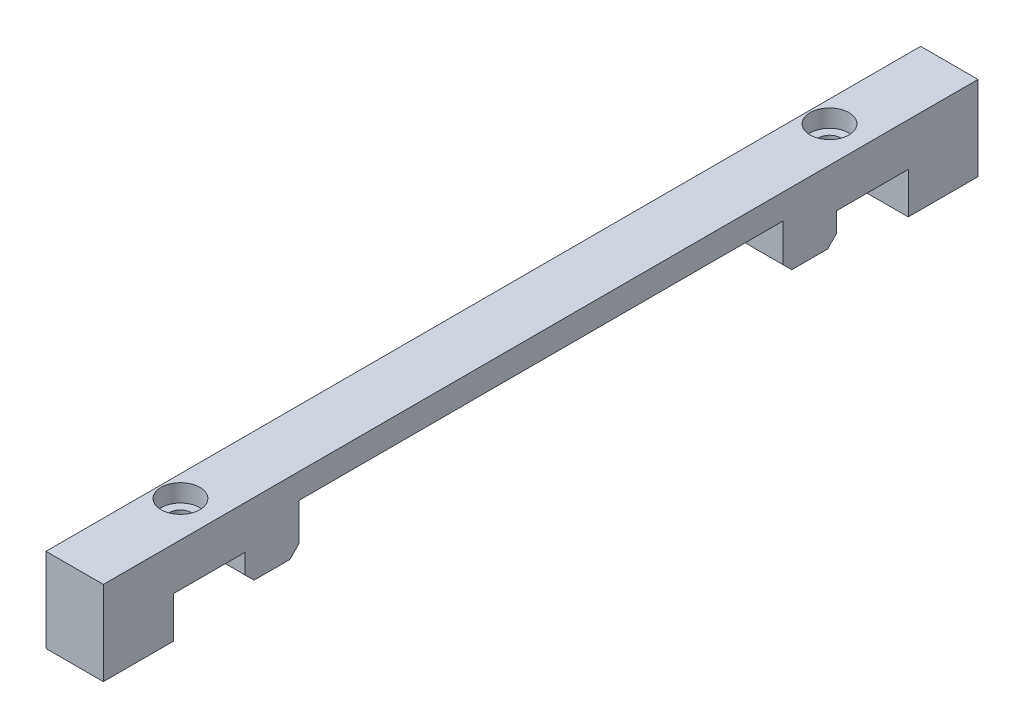
SolidWorks part; units mm, degrees
ref_plane "Front Plane" through (0, 0, 0) normal (0, 0, 1) x (1, 0, 0)
ref_plane "Top Plane" through (0, 0, 0) normal (0, 1, 0) x (1, 0, 0)
ref_plane "Right Plane" through (0, 0, 0) normal (1, 0, 0) x (0, 0, -1)
sketch "Sketch1" plane through (0, 0, 0) normal (0, 1, 0) x (1, 0, 0)
  line L1 (-4.064, 63.5) -> (4.064, 63.5)
  line L2 (-4.064, 63.5) -> (-4.064, -63.5)
  line L3 (-4.064, -63.5) -> (4.064, -63.5)
  line L4 (4.064, 63.5) -> (4.064, -63.5)
  line L5 (-4.064, 63.5) -> (4.064, -63.5) construction
  line L6 (-4.064, -63.5) -> (4.064, 63.5) construction
  point P0 (0, 0)
  dimension "D1" = 127
  dimension "D2" = 8.128
extrude "Boss-Extrude1" add sketch "Sketch1" along normal blind 18.288
sketch "Sketch2" plane through (0, 0, 0) normal (0, -1, 0) x (1, 0, 0)
  line L0 (4.064, 63.5) -> (4.064, -63.5) construction
  line L1 (-4.064, 52.07) -> (4.064, 52.07)
  line L2 (-4.064, 52.07) -> (-4.064, -52.07)
  line L3 (-4.064, -52.07) -> (4.064, -52.07)
  line L4 (4.064, 52.07) -> (4.064, -52.07)
  line L5 (-4.064, 52.07) -> (4.064, -52.07) construction
  line L6 (-4.064, -52.07) -> (4.064, 52.07) construction
  point P0 (0, 0)
  dimension "D1" = 104.14
extrude "Cut-Extrude1" cut sketch "Sketch2" against normal blind 8.128
sketch "Sketch4" plane through (0, 8.128, 0) normal (0, -1, 0) x (1, 0, 0)
  line L1 (-4.064, -41.91) -> (4.064, -41.91)
  line L2 (-4.064, -41.91) -> (-4.064, -52.07)
  line L3 (-4.064, -52.07) -> (4.064, -52.07)
  line L4 (4.064, -41.91) -> (4.064, -52.07)
  line L5 (-4.064, -41.91) -> (4.064, -52.07) construction
  line L6 (-4.064, -52.07) -> (4.064, -41.91) construction
  point P0 (0, -46.99)
  dimension "D1" = 10.16
extrude "Cut-Extrude2" cut sketch "Sketch4" against normal blind 4.064
sketch "Sketch5" plane through (0, 8.128, 0) normal (0, -1, 0) x (1, 0, 0)
  line L0 (4.064, -41.91) -> (4.064, 52.07) construction
  line L5 (4.064, 0) -> (-4.064, 0)
  line L6 (4.064, 0) -> (4.064, -34.29)
  line L8 (4.064, -34.29) -> (-4.064, -34.29)
  line L9 (-4.064, 0) -> (-4.064, -34.29)
  line L10 (4.064, -41.91) -> (-4.064, -41.91) construction
  dimension "D1" = 7.62
extrude "Cut-Extrude4" cut sketch "Sketch5" against normal blind 6.604
sketch "Sketch6" plane through (0, 18.288, 0) normal (0, 1, 0) x (1, 0, 0)
  line L1 (4.064, -63.5) -> (4.064, 63.5) construction
  line L3 (-4.064, 52.07) -> (4.064, 52.07) construction
  point P0 (-1.016, 46.99)
  dimension "D1" = 5.08
  dimension "D2" = 5.08
hole_wizard "CBORE for M2.5 SHCS1" positions "Sketch7" profile "Sketch8" counterbore size "M2.5" standard "ANSI Metric" end condition through all
sketch "Sketch7" plane through (0, 18.288, 0) normal (0, 1, 0) x (1, 0, 0)
  line L0 (4.064, -63.5) -> (4.064, 63.5) construction
  line L5 (-4.064, 45.99) -> (4.064, 45.99) construction
  line L9 (-4.064, 52.07) -> (4.064, 52.07) construction
  point P0 (-1.016, 45.99)
  dimension "D1" = 5.08
  dimension "D2" = 6.08
sketch "Sketch8" plane through (-1.016, 18.288, -45.99) normal (1, 0, 0) x (0, 0, 1)
  line L0 (0, 0) -> (0, 18.288)
  line L1 (0, 18.288) -> (1.55, 18.288)
  line L3 (1.55, 18.288) -> (1.55, 2.5)
  line L4 (1.55, 2.5) -> (2.75, 2.5)
  line L5 (2.75, 2.5) -> (2.75, 0)
  line L7 (2.75, 0) -> (0, 0)
  line L11 (0, -6.35) -> (0, 107.95) construction
  dimension "Thru Hole Dia." = 3.1
  dimension "Thru Hole Depth" = 18.288
  dimension "C'Bore Dia." = 5.5
  dimension "C'Bore Depth" = 2.5
mirror "Mirror1" about plane through (4.064, 14.732, 0) normal (0, 0, 1) of "Cut-Extrude4", "Cut-Extrude2"
mirror "Mirror2" about plane through (0, 0, 0) normal (0, 0, 1) of "CBORE for M2.5 SHCS1"
sketch "Sketch11" plane through (0, 0, 0) normal (0, -1, 0) x (1, 0, 0)
  line L0 (4.064, -57.785) -> (-4.064, -57.785) construction
  line L1 (4.064, -52.07) -> (4.064, -63.5) construction
  line L2 (-4.064, -63.5) -> (-4.064, -52.07) construction
  line L3 (0, -52.07) -> (0, -63.5) construction
  line L4 (-4.064, -52.07) -> (4.064, -52.07) construction
  line L5 (4.064, -63.5) -> (-4.064, -63.5) construction
  point P12 (0, -57.785)
hole_wizard "Ø1.0mm Dowel Hole1" positions "Sketch16" profile "Sketch15" hole size "Ø1.0" standard "ANSI Metric"
sketch "Sketch16" plane through (0, 0, 0) normal (0, -1, 0) x (-1, 0, 0)
  line L0 (-4.064, 57.785) -> (4.064, 57.785) construction
  line L1 (-4.064, 52.07) -> (-4.064, 63.5) construction
  line L2 (4.064, 63.5) -> (4.064, 52.07) construction
  line L4 (0, 63.5) -> (0, 52.07) construction
  line L5 (-4.064, 63.5) -> (4.064, 63.5) construction
  line L6 (4.064, 52.07) -> (-4.064, 52.07) construction
  point P0 (0, 57.785)
sketch "Sketch15" plane through (0, 0, -57.785) normal (1, 0, 0) x (0, 0, -1)
  line L0 (0, 0) -> (0, 11.9423)
  line L1 (0, 11.9423) -> (2.65, 10.35)
  line L2 (2.65, 10.35) -> (2.65, 0)
  line L5 (2.65, 0) -> (0, 0)
  line L10 (0, 11.9423) -> (-2.65, 10.35) construction
  line L11 (0, -6.35) -> (0, 107.95) construction
  dimension "Hole Dia." = 5.3
  dimension "Hole Depth" = 10.35
  dimension "Drill Angle" = 118
mirror "Mirror3" about plane through (0, 0, 0) normal (0, 0, 1) of "Ø1.0mm Dowel Hole1"
chamfer "Chamfer1" distance 1.27 angle 45 8 edges at (0, 0, 52.07) (0, 0, 63.5) (0, 8.128, 34.29) (0, 8.128, 41.91) (0, 8.128, -34.29) (0, 8.128, -41.91) (0, 0, -63.5) (0, 0, -52.07)
sketch "Sketch17" plane through (0, 0, 0) normal (0, -1, 0) x (1, 0, 0)
  line L5 (-4.064, 63.5) -> (4.064, 63.5)
  line L6 (-4.064, 63.5) -> (-4.064, -63.5)
  line L7 (-4.064, -63.5) -> (4.064, -63.5)
  line L8 (4.064, 63.5) -> (4.064, -63.5)
extrude "Cut-Extrude5" cut sketch "Sketch17" against normal blind 6.35
sketch "Sketch18" plane through (0, 6.35, 0) normal (0, -1, 0) x (1, 0, 0)
  line L0 (4.064, -63.5) -> (4.064, -61.9536)
  line L1 (4.064, -63.5) -> (4.064, -52.07) construction
  line L2 (4.064, -61.9536) -> (-4.064, -61.9536)
  line L3 (-4.064, -52.07) -> (-4.064, -63.5) construction
  line L4 (-4.064, -61.9536) -> (-4.064, -63.5)
  line L5 (-4.064, -63.5) -> (4.064, -63.5)
extrude "Cut-Extrude6" cut sketch "Sketch18" against normal through all
sketch "Sketch19" plane through (0, 6.35, 0) normal (0, -1, 0) x (1, 0, 0)
  line L0 (4.064, 63.5) -> (4.064, 61.9923)
  line L1 (4.064, 52.07) -> (4.064, 63.5) construction
  line L2 (4.064, 61.9923) -> (-4.064, 61.9923)
  line L3 (-4.064, 63.5) -> (-4.064, 52.07) construction
  line L4 (-4.064, 61.9923) -> (-4.064, 63.5)
  line L5 (-4.064, 63.5) -> (4.064, 63.5)
extrude "Cut-Extrude7" cut sketch "Sketch19" against normal through all
